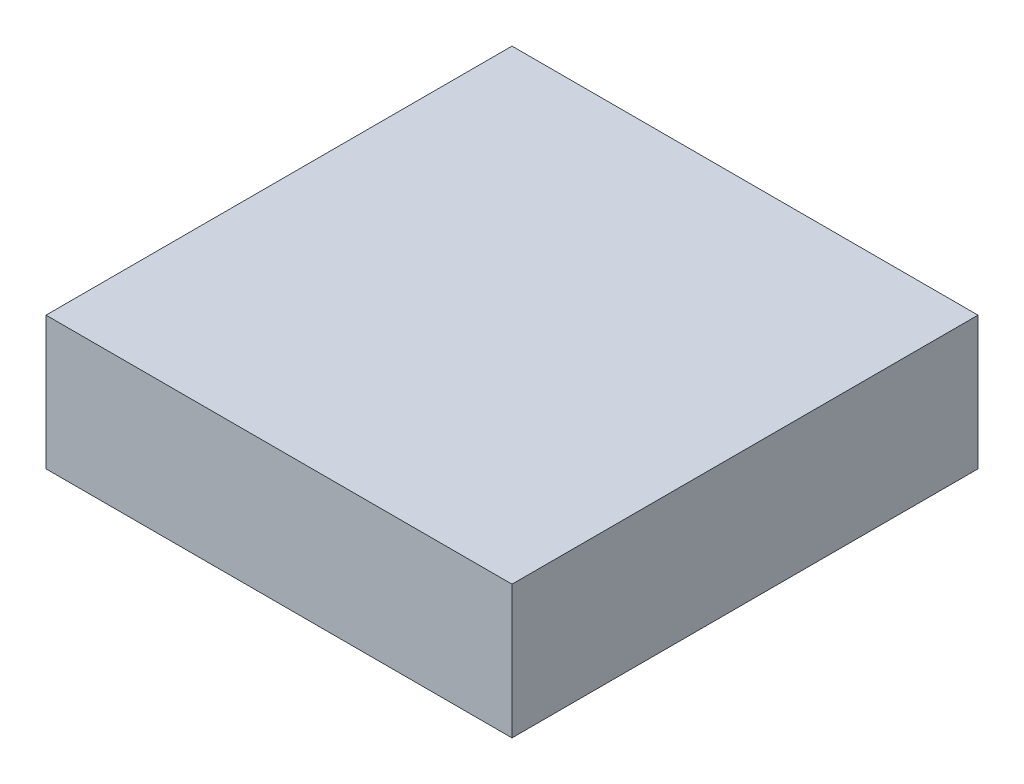
SolidWorks part; units mm, degrees
ref_plane "Front Plane" through (0, 0, 0) normal (0, 0, 1) x (1, 0, 0)
ref_plane "Top Plane" through (0, 0, 0) normal (0, 1, 0) x (1, 0, 0)
ref_plane "Right Plane" through (0, 0, 0) normal (1, 0, 0) x (0, 0, -1)
sketch "ProfileS" plane through (0, 0, 0) normal (0, 1, 0) x (1, 0, 0)
  line L1 (-1.75, 1.75) -> (1.75, 1.75)
  line L2 (-1.75, 1.75) -> (-1.75, -1.75)
  line L3 (-1.75, -1.75) -> (1.75, -1.75)
  line L4 (1.75, 1.75) -> (1.75, -1.75)
  line L5 (-1.75, 1.75) -> (1.75, -1.75) construction
  line L6 (-1.75, -1.75) -> (1.75, 1.75) construction
  point P0 (0, 0)
  dimension "Width" = 3.5
  dimension "Length" = 3.5
extrude "Profile" add sketch "ProfileS" along normal blind 1
sketch "Sketch1" plane through (0, 0, 0) normal (1, 0, 0) x (0, 0, -1)
  line L0 (0, 0.9) -> (1.5, 0.9)
  line L1 (1.5, 0.9) -> (1.3, 0.2)
  line L2 (1.3, 0.2) -> (0, 0.2)
  line L3 (0, 0.2) -> (0, 0.9)
  line L4 (0, 0) -> (0, 0.2) construction
  line L5 (-1.75, 1) -> (1.75, 1) construction
  dimension "D1" = 0.2
  dimension "D2" = 0.2
  dimension "D3" = 0.1
  dimension "D4" = 3
revolve "Cut-Revolve1" cut sketch "Sketch1" angle 360 about L4
